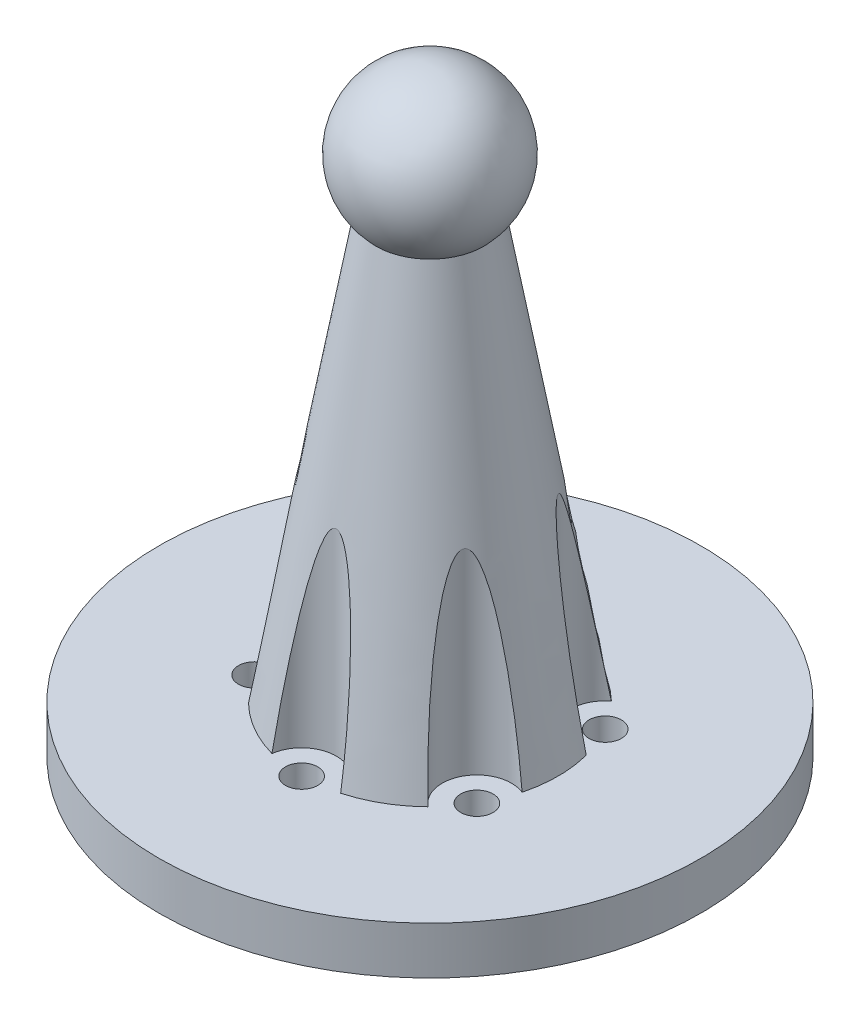
SolidWorks part; units mm, degrees
ref_plane "前视基准面" through (0, 0, 0) normal (0, 0, 1) x (1, 0, 0)
ref_plane "上视基准面" through (0, 0, 0) normal (0, 1, 0) x (1, 0, 0)
ref_plane "右视基准面" through (0, 0, 0) normal (1, 0, 0) x (0, 0, -1)
sketch "草图1" plane through (0, 0, 0) normal (0, 1, 0) x (1, 0, 0)
  circle A0 centre (0, 0) radius 13.5 construction
  circle A1 centre (0, 0) radius 28.5
  circle A2 centre (0, 13.5) radius 1.7
  circle A3 centre (11.6913, 6.75) radius 1.7
  circle A4 centre (11.6913, -6.75) radius 1.7
  circle A5 centre (0, -13.5) radius 1.7
  circle A6 centre (-11.6913, -6.75) radius 1.7
  circle A7 centre (-11.6913, 6.75) radius 1.7
  point P18 (0, 0)
  dimension "D1" = 27
  dimension "D2" = 57
  dimension "D3" = 3.4
  dimension "D4" = 6
extrude "凸台-拉伸1" add sketch "草图1" along normal blind 5
sketch "草图2" plane through (0, 5, 0) normal (0, 1, 0) x (1, 0, 0)
  circle A0 centre (0, 0) radius 13.5
  dimension "D1" = 27
extrude "凸台-拉伸2" add sketch "草图2" along normal blind 50 draft 10
sketch "草图3" plane through (0, 5, 0) normal (0, -1, 0) x (1, 0, 0)
  circle A0 centre (-11.6913, -6.75) radius 3.65
  arc A1 (-12.447, -5.2272) -> (-10.7503, -8.1658) centre (0, 0) ccw construction
  circle A2 centre (-11.6913, 6.75) radius 3.65
  circle A3 centre (0, 13.5) radius 3.65
  circle A4 centre (11.6913, 6.75) radius 3.65
  circle A5 centre (11.6913, -6.75) radius 3.65
  circle A6 centre (0, -13.5) radius 3.65
  point P18 (0, 0)
  dimension "D1" = 7.3
  dimension "D2" = 6
extrude "切除-拉伸1" cut sketch "草图3" against normal blind 50
sketch "草图4" plane through (0, 55, 0) normal (0, 1, 0) x (1, 0, 0)
  line L0 (0, 8) -> (0, -8)
  arc A0 (0, -8) -> (0, 8) centre (0, 0) ccw
  dimension "D1" = 16
revolve "旋转5" add sketch "草图4" angle 360 about L0
